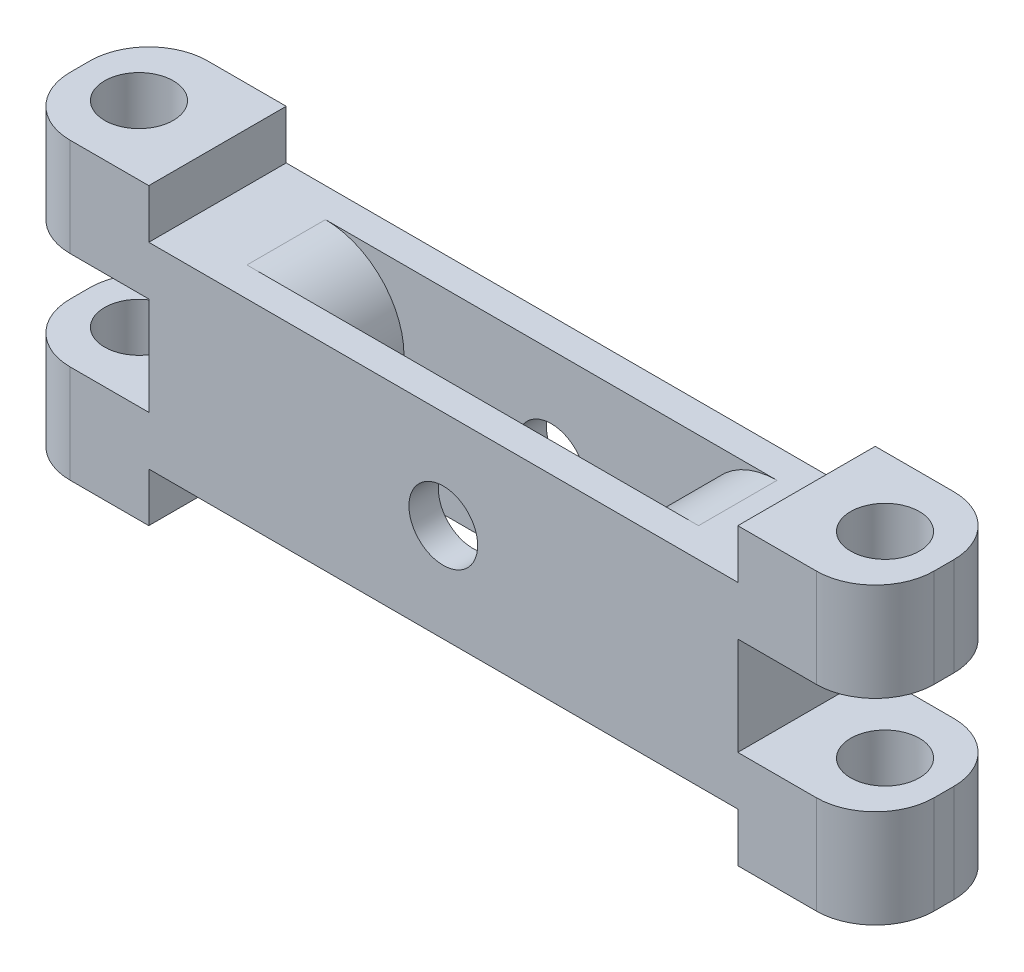
SolidWorks part; units mm, degrees
ref_plane "Front Plane" through (0, 0, 0) normal (0, 0, 1) x (1, 0, 0)
ref_plane "Top Plane" through (0, 0, 0) normal (0, 1, 0) x (1, 0, 0)
ref_plane "Right Plane" through (0, 0, 0) normal (1, 0, 0) x (0, 0, -1)
sketch "Sketch1" plane through (0, 0, 0) normal (0, 1, 0) x (1, 0, 0)
  line L1 (-15, 3.5) -> (15, 3.5)
  line L2 (-15, 3.5) -> (-15, -3.5)
  line L3 (-15, -3.5) -> (15, -3.5)
  line L4 (15, 3.5) -> (15, -3.5)
  line L5 (-15, 3.5) -> (15, -3.5) construction
  line L6 (-15, -3.5) -> (15, 3.5) construction
  point P0 (0, 0)
  dimension "D1" = 7
  dimension "D2" = 30
extrude "Boss-Extrude1" add sketch "Sketch1" along normal blind 10
sketch "Sketch2" plane through (0, 10, 0) normal (0, 1, 0) x (1, 0, 0)
  line L1 (-7.5, 2) -> (7.5, 2)
  line L2 (-7.5, 2) -> (-7.5, -2)
  line L3 (-7.5, -2) -> (7.5, -2)
  line L4 (7.5, 2) -> (7.5, -2)
  line L5 (-7.5, 2) -> (7.5, -2) construction
  line L6 (-7.5, -2) -> (7.5, 2) construction
  point P0 (0, 0)
  dimension "D1" = 15
  dimension "D2" = 4
extrude "Cut-Extrude1" cut sketch "Sketch2" against normal blind 10
sketch "Sketch3" plane through (0, 0, 3.5) normal (0, 0, 1) x (1, 0, 0)
  line L0 (-15, 5) -> (0, 5) construction
  line L1 (-15, 10) -> (-15, 0) construction
  line L2 (0, 5) -> (0, 0) construction
  circle A0 centre (0, 5) radius 1.75
  dimension "D1" = 3.5
extrude "Cut-Extrude2" cut sketch "Sketch3" against normal blind 10
fillet "Fillet1" radius 4 4 edges at (-7.5, 0, 0) (-7.5, 10, 0) (7.5, 10, 0) (7.5, 0, 0)
sketch "Sketch4" plane through (15, 0, 0) normal (1, 0, 0) x (0, 0, -1)
  line L0 (-3.5, 5) -> (0, 5) construction
  line L1 (-3.5, -2.5) -> (3.5, -2.5)
  line L2 (-3.5, -2.5) -> (-3.5, 12.5)
  line L3 (-3.5, 12.5) -> (3.5, 12.5)
  line L4 (3.5, -2.5) -> (3.5, 12.5)
  line L5 (-3.5, -2.5) -> (3.5, 12.5) construction
  line L6 (-3.5, 12.5) -> (3.5, -2.5) construction
  line L7 (-3.5, 10) -> (-3.5, 0) construction
  line L8 (0, 5) -> (0, 0) construction
  point P0 (0, 5)
  point P9 (-4.1022, 11.488)
  dimension "D1" = 15
extrude "Boss-Extrude2" add sketch "Sketch4" along normal blind 7
sketch "Sketch5" plane through (22, 0, 0) normal (1, 0, 0) x (0, 0, -1)
  line L0 (-3.5, 5) -> (0, 5) construction
  line L1 (3.5, -2.5) -> (3.5, 12.5) construction
  line L2 (-3.5, 12.5) -> (-3.5, -2.5) construction
  line L3 (0, 5) -> (0, 0) construction
  line L4 (-3.5, 7.5) -> (3.5, 7.5)
  line L5 (-3.5, 7.5) -> (-3.5, 2.5)
  line L6 (-3.5, 2.5) -> (3.5, 2.5)
  line L7 (3.5, 7.5) -> (3.5, 2.5)
  line L8 (-3.5, 7.5) -> (3.5, 2.5) construction
  line L9 (-3.5, 2.5) -> (3.5, 7.5) construction
  dimension "D1" = 5
extrude "Cut-Extrude3" cut sketch "Sketch5" against normal blind 7
sketch "Sketch6" plane through (0, 12.5, 0) normal (0, 1, 0) x (1, 0, 0)
  line L0 (22, 0) -> (19, 0) construction
  line L1 (22, 3.5) -> (22, -3.5) construction
  circle A0 centre (19, 0) radius 1.75
  dimension "D2" = 3.5
  dimension "D1" = 3
extrude "Cut-Extrude4" cut sketch "Sketch6" against normal through all
fillet "Fillet2" radius 3 4 edges at (22, 10, 3.5) (22, 10, -3.5) (22, 0, 3.5) (22, 0, -3.5)
mirror "Mirror1" about plane through (0, 0, 0) normal (1, 0, 0) of "Fillet2", "Cut-Extrude4", "Cut-Extrude3", "Boss-Extrude2"
